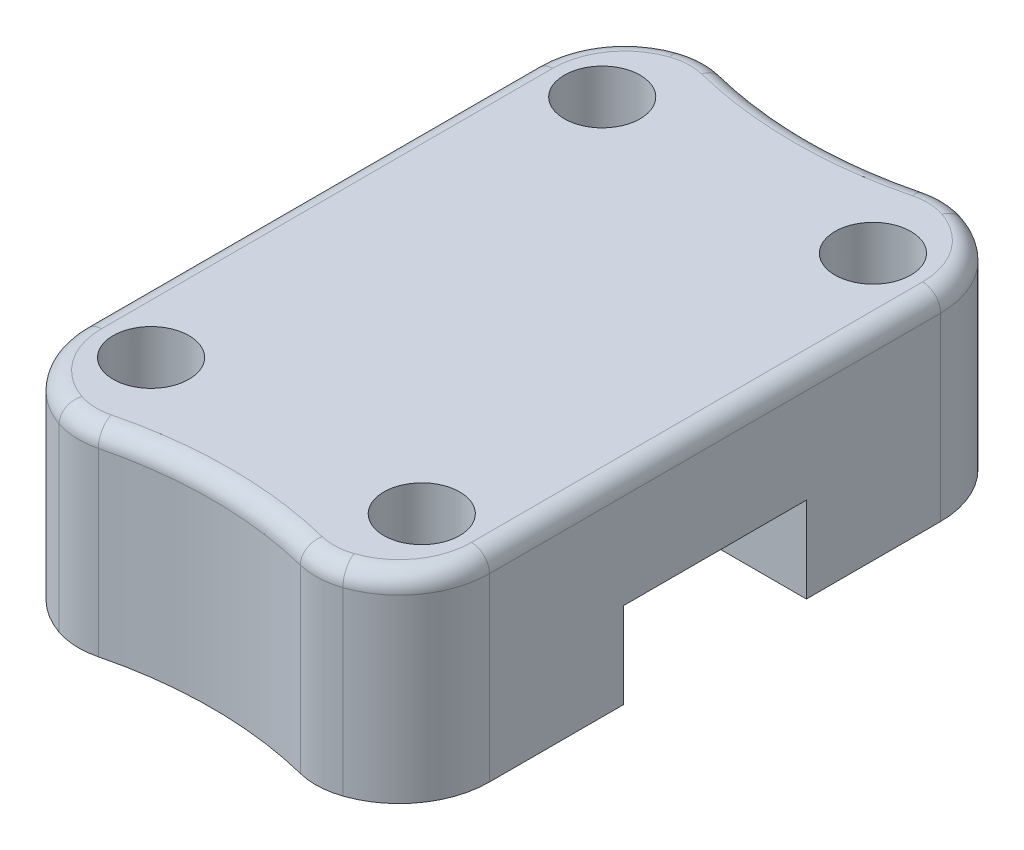
SolidWorks part; units mm, degrees
ref_plane "Спереди" through (0, 0, 0) normal (0, 0, 1) x (1, 0, 0)
ref_plane "Сверху" through (0, 0, 0) normal (0, 1, 0) x (1, 0, 0)
ref_plane "Справа" through (0, 0, 0) normal (1, 0, 0) x (0, 0, -1)
sketch "Sketch1" plane through (0, 0, 0) normal (0, 1, 0) x (1, 0, 0)
  line L1 (22.5, -35) -> (-22.5, -35)
  line L2 (22.5, -35) -> (22.5, 35)
  line L3 (22.5, 35) -> (-22.5, 35)
  line L4 (-22.5, -35) -> (-22.5, 35)
  line L5 (22.5, -35) -> (-22.5, 35) construction
  line L6 (22.5, 35) -> (-22.5, -35) construction
  point P0 (0, 0)
  dimension "D1" = 45
  dimension "D2" = 70
extrude "Boss-Extrude1" add sketch "Sketch1" along normal blind 22
sketch "Sketch2" plane through (22.5, 0, 0) normal (1, 0, 0) x (0, 0, -1)
  line L0 (0, 0) -> (0, 22) construction
  line L1 (-35, 0) -> (35, 0) construction
  line L2 (-35, 22) -> (35, 22) construction
  line L4 (10.125, 9.5) -> (-10.125, 9.5)
  line L5 (10.125, 9.5) -> (10.125, 0)
  line L6 (10.125, 0) -> (-10.125, 0)
  line L7 (-10.125, 9.5) -> (-10.125, 0)
  line L8 (10.125, 9.5) -> (-10.125, 0) construction
  line L9 (10.125, 0) -> (-10.125, 9.5) construction
  point P6 (0, 4.75)
  dimension "D1" = 20.25
  dimension "D2" = 9.5
extrude "Cut-Extrude1" cut sketch "Sketch2" against normal through all and the other way through all
sketch "Sketch3" plane through (0, 0, 0) normal (0, -1, 0) x (1, 0, 0)
  line L0 (15, -25) -> (15, 25) construction
  line L1 (-15, 25) -> (-15, -25) construction
  line L2 (-15, -25) -> (15, 25) construction
  line L3 (-22.5, -25) -> (22.5, -25) construction
  line L4 (-22.5, -35) -> (-22.5, -10.125) construction
  line L5 (22.5, -10.125) -> (22.5, -35) construction
  line L6 (-22.5, 25) -> (22.5, 25) construction
  line L7 (-22.5, 10.125) -> (-22.5, 35) construction
  line L8 (22.5, 35) -> (22.5, 10.125) construction
  line L9 (-15, 25) -> (15, -25) construction
  circle A0 centre (15, 25) radius 4.2
  circle A1 centre (15, -25) radius 4.2
  circle A2 centre (-15, -25) radius 4.2
  circle A3 centre (-15, 25) radius 4.2
  point P4 (0, 0)
  dimension "D1" = 8.4
  dimension "D2" = 30
  dimension "D3" = 50
extrude "Cut-Extrude2" cut sketch "Sketch3" against normal through all
fillet "Fillet1" radius 10 4 edges at (-22.5, 11, 35) (22.5, 11, 35) (-22.5, 11, -35) (22.5, 11, -35)
sketch "Sketch6" plane through (0, 0, 0) normal (0, -1, 0) x (1, 0, 0)
  line L0 (12.5, 35) -> (-12.5, 35)
  line L1 (12.5, -35) -> (-12.5, -35)
  arc A0 (12.5, -35) -> (-12.5, -35) centre (0, -79.2691) ccw
  arc A1 (12.5, 35) -> (-12.5, 35) centre (0, 79.2691) cw
  dimension "D1" = 46
extrude "Cut-Extrude3" cut sketch "Sketch6" against normal through all
fillet "Fillet2" radius 8 4 edges at (-12.5, 11, -35) (12.5, 11, -35) (12.5, 11, 35) (-12.5, 11, 35)
fillet "Fillet4" radius 2 12 edges at (-20.631, 22, -30.8212) (-13.4734, 22, -34.8865) (0, 22, -33.2691) (13.4734, 22, -34.8865) (20.631, 22, -30.8212) (22.5, 22, 0) (20.631, 22, 30.8212) (13.4734, 22, 34.8865) (0, 22, 33.2691) (-13.4734, 22, 34.8865) (-20.631, 22, 30.8212) (-22.5, 22, 0)
chamfer "Chamfer1" distance 0.5 angle 70 4 edges at (-15, 0, 20.8) (15, 0, 20.8) (-15, 0, -29.2) (15, 0, -29.2)
